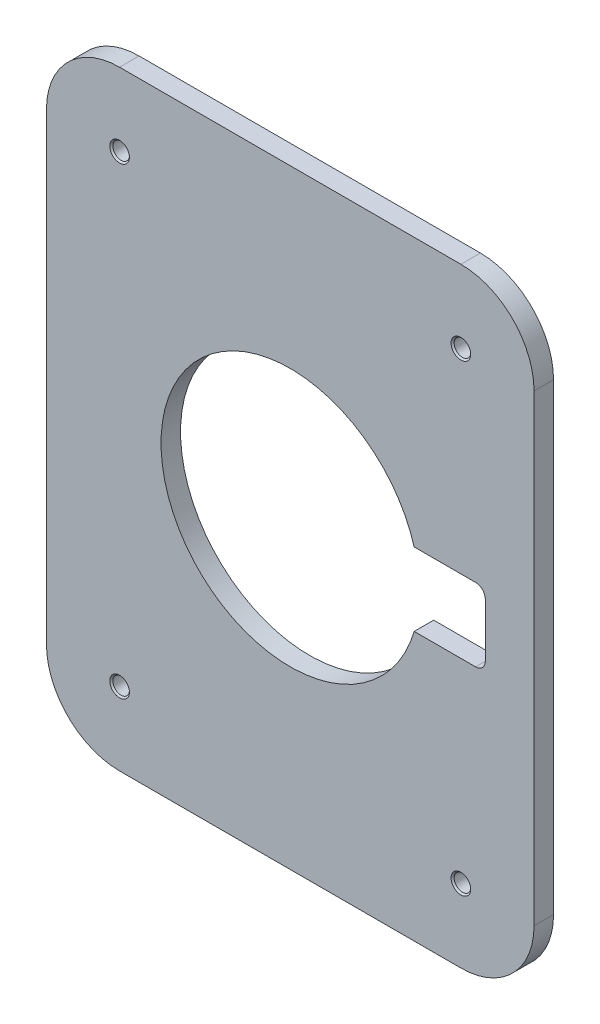
SolidWorks part; units mm, degrees
material "1.4301 (X5CrNi18-10)"
ref_plane "Ebene vorne" through (0, 0, 0) normal (0, 0, 1) x (1, 0, 0)
ref_plane "Ebene oben" through (0, 0, 0) normal (0, 1, 0) x (1, 0, 0)
ref_plane "Ebene rechts" through (0, 0, 0) normal (1, 0, 0) x (0, 0, -1)
sketch "Skizze1" plane through (0, 0, 0) normal (0, 0, 1) x (1, 0, 0)
  line L0 (50.8331, 15) -> (80, 15)
  line L1 (-100, 125) -> (100, 125)
  line L2 (-100, 125) -> (-100, -125)
  line L3 (-100, -125) -> (100, -125)
  line L4 (100, 125) -> (100, -125)
  line L5 (-100, 125) -> (100, -125) construction
  line L6 (-100, -125) -> (100, 125) construction
  line L7 (80, 15) -> (80, -15)
  line L8 (80, -15) -> (50.8331, -15)
  line L9 (0, 0) -> (129.7438, 0) construction
  arc A0 (50.8331, 15) -> (50.8331, -15) centre (0, 0) ccw
  dimension "D1" = 106
  dimension "D2" = 250
  dimension "D3" = 200
  dimension "D4" = 30
  dimension "D5" = 20
extrude "Aufsatz-Linear austragen1" add sketch "Skizze1" along normal blind 8 contours L4 L3 L2 L1
fillet "Verrundung1" radius 30 4 edges at (100, 125, 4) (-100, 125, 4) (-100, -125, 4) (100, -125, 4)
fillet "Verrundung2" radius 4 2 edges at (80, -15, 4) (80, 15, 4)
hole_wizard "M8 Gewindebohrung1" positions "Skizze2" profile "Skizze3" tap size "M8" standard "DIN" end condition through all
sketch "Skizze2" plane through (0, 0, 0) normal (0, 0, -1) x (-1, 0, 0)
  arc A0 (-70, 125) -> (-100, 95) centre (-70, 95) ccw construction
  arc A1 (100, 95) -> (70, 125) centre (70, 95) ccw construction
  arc A2 (70, -125) -> (100, -95) centre (70, -95) ccw construction
  arc A3 (-100, -95) -> (-70, -125) centre (-70, -95) ccw construction
  point P0 (-70, 95)
  point P2 (70, 95)
  point P4 (70, -95)
  point P6 (-70, -95)
sketch "Skizze3" plane through (70, 95, 0) normal (1, 0, 0) x (0, 1, 0)
  line L0 (0, 0) -> (0, 8)
  line L1 (0, 8) -> (4.025, 8)
  line L2 (3.4, 7.375) -> (3.4, 0.625)
  line L3 (3.4, 0.625) -> (4.025, 0)
  line L5 (4.025, 0) -> (0, 0)
  line L6 (-3.4, 0.625) -> (-4.025, 0) construction
  line L7 (4.025, 8) -> (3.4, 7.375)
  line L8 (-4.025, 8) -> (-3.4, 7.375) construction
  line L11 (0, -6.35) -> (0, 107.95) construction
  dimension "Bohrerdurchmesser" = 6.8
  dimension "Bohrungstiefe" = 8
  dimension "Senkdurchmesser (Oben)" = 8.05
  dimension "Senkwinkel (Oben)" = 90
  dimension "Senkdurchmesser (Unten)" = 8.05
  dimension "Senkwinkel (Unten)" = 90
cosmetic thread "Bohrungsgewinde1" parameters "D2"=8
cosmetic thread "Bohrungsgewinde2" parameters "D2"=8
cosmetic thread "Bohrungsgewinde3" parameters "D2"=8
cosmetic thread "Bohrungsgewinde4" parameters "D2"=8
